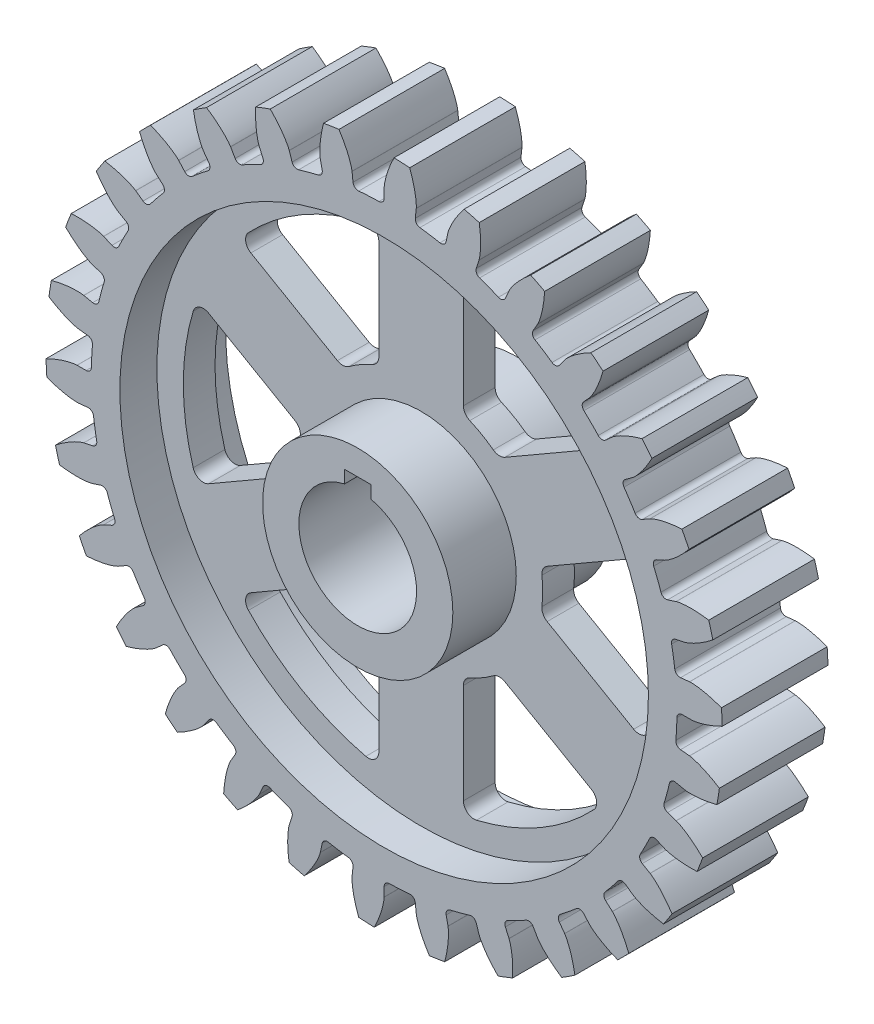
SolidWorks part; units mm, degrees
ref_plane "Front Plane" through (0, 0, 0) normal (0, 0, 1) x (1, 0, 0)
ref_plane "Top Plane" through (0, 0, 0) normal (0, 1, 0) x (1, 0, 0)
ref_plane "Right Plane" through (0, 0, 0) normal (1, 0, 0) x (0, 0, -1)
sketch "Sketch1" plane through (0, 0, 0) normal (1, 0, 0) x (0, 0, -1)
  line L0 (-19.05, 0) -> (19.05, 0)
  line L1 (19.05, 0) -> (19.05, 22.86)
  line L2 (19.05, 22.86) -> (3.81, 22.86)
  line L3 (3.81, 22.86) -> (3.81, 63.5)
  line L4 (3.81, 63.5) -> (12.7, 63.5)
  line L5 (12.7, 63.5) -> (12.7, 70.358)
  line L6 (12.7, 70.358) -> (-12.7, 70.358)
  line L7 (0, 55) -> (0, -55) construction
  line L8 (55, 0) -> (-55, 0) construction
  line L9 (0, 0) -> (0, 70.358) construction
  line L10 (-19.05, 0) -> (-19.05, 22.86)
  line L11 (-19.05, 22.86) -> (-3.81, 22.86)
  line L12 (-3.81, 22.86) -> (-3.81, 63.5)
  line L13 (-3.81, 63.5) -> (-12.7, 63.5)
  line L14 (-12.7, 63.5) -> (-12.7, 70.358)
  dimension "D1" = 3.81
  dimension "D2" = 63.5
  dimension "D3" = 70.358
  dimension "D4" = 12.7
ref_axis "Axis1" through (0, 0, 20.955) along (0, 0, -1)
revolve "Revolve1" add sketch "Sketch1" angle 360 about axis through (0, 0, 20.955) along (0, 0, -1)
sketch "Sketch2" plane through (0, 0, 0) normal (0, 0, 1) x (1, 0, 0)
  line L0 (73.787, 0) -> (70.358, 0)
  line L1 (0, 0) -> (94.0494, 4.9289) construction
  line L2 (73.3828, 7.7128) -> (69.9726, 7.3544)
  arc A0 (81.2453, 2.3735) -> (81.0484, 6.132) centre (0, 0) ccw
  circle A1 centre (0, 0) radius 70.358 construction
  arc A2 (70.358, 0) -> (69.9726, 7.3544) centre (0, 0) ccw
  spline S0 degree 4 poles (73.787, 0) (73.8416, 0.0012) (73.9944, 0.008) (74.2828, 0.0349) (74.7515, 0.0989) (75.345, 0.2096) (76.1065, 0.3861) (76.9949, 0.6365) (77.9608, 0.9559) (78.9981, 1.3503) (80.0202, 1.7854) (81.0261, 2.2568) (82.0158, 2.7611) (83.1972, 3.4098) (84.592, 4.2449) (86.1811, 5.2931) (87.9419, 6.5808) (89.6733, 7.9733) (91.3432, 9.4391) (92.7509, 10.7796) (93.9201, 11.967) (94.8691, 12.9798) (95.614, 13.8045) (96.5255, 14.8499) (97.4145, 15.9197) (98.1892, 16.8948) (98.8659, 17.7823) (99.359, 18.4422) (99.8613, 19.1329) (100.322, 19.7792) (100.825, 20.5115) (101.2452, 21.1308) (101.7679, 21.9265) (102.1191, 22.4721) (102.7345, 23.4529) (103.1421, 24.1299) (103.5488, 24.8103) (103.7468, 25.157) (103.8765, 25.3798) knots 0 0 0 0 0 0.005377 0.015084 0.028532 0.04661 0.064855 0.092111 0.119476 0.146842 0.174209 0.201575 0.228941 0.256307 0.307035 0.361767 0.4165 0.471232 0.525964 0.580697 0.608063 0.635429 0.662795 0.690161 0.744894 0.77226 0.785943 0.799626 0.826992 0.854358 0.868042 0.881725 0.909091 0.931818 0.954545 0.977273 1 1 1 1 1 construction
  spline S1 degree 4 poles (73.787, 0) (73.8416, 0.0012) (73.9944, 0.008) (74.2828, 0.0349) (74.7515, 0.0989) (75.345, 0.2096) (76.1065, 0.3861) (76.9949, 0.6365) (77.9608, 0.9559) (78.9981, 1.3503) (79.9496, 1.7554) (80.6354, 2.074) (81.0655, 2.2839) (81.2453, 2.3735) knots 0 0 0 0 0 0.005377 0.015084 0.028532 0.04661 0.064855 0.092111 0.119476 0.146842 0.174209 0.194009 0.194009 0.194009 0.194009 0.194009
  spline S2 degree 4 poles (73.3828, 7.7128) (73.4372, 7.7174) (73.5899, 7.7266) (73.8795, 7.7299) (74.3523, 7.7153) (74.9541, 7.6672) (75.7299, 7.5713) (76.6397, 7.4152) (77.6336, 7.1984) (78.7065, 6.9146) (79.6951, 6.6113) (80.4105, 6.366) (80.8602, 6.2022) (81.0484, 6.132) knots 0 0 0 0 0 0.005377 0.015084 0.028532 0.04661 0.064855 0.092111 0.119476 0.146842 0.174209 0.194009 0.194009 0.194009 0.194009 0.194009
extrude "Boss-Extrude1" add sketch "Sketch2" along normal up to surface and the other way up to surface contours S2 A0 S1 L0 A2 L2
fillet "Fillet5" radius 1.27 2 edges at (73.3828, 7.7128, 0) (69.9726, 7.3544, 0)
fillet "Fillet6" radius 1.27 2 edges at (73.787, 0, 0) (70.358, 0, 0)
pattern_circular "CirPattern2" count 30 over 360 about axis through (0, 0, 20.955) along (0, 0, -1) of "Boss-Extrude1", "Fillet5", "Fillet6"
sketch "Sketch3" plane through (0, 0, 0) normal (0, 0, 1) x (1, 0, 0)
  line L0 (0, 16.83) -> (3.175, 16.83)
  line L1 (0, -20.955) -> (0, 20.955) construction
  line L2 (0, 16.83) -> (-3.175, 16.83)
  line L3 (3.175, 16.83) -> (3.175, 13.782)
  line L4 (-3.175, 16.83) -> (-3.175, 13.782)
  arc A0 (-3.175, 13.782) -> (3.175, 13.782) centre (0, 0) ccw
extrude "Cut-Extrude2" cut sketch "Sketch3" against normal through all and the other way through all
sketch "Sketch4" plane through (0, 0, 0) normal (0, 0, 1) x (1, 0, 0)
  line L0 (10.16, 45.3436) -> (10.16, 32.6436)
  line L2 (0, -20.955) -> (0, 20.955) construction
  line L3 (0, 0) -> (93.946, 54.2398) construction
  line L4 (36.8269, 32.9938) -> (21.429, 24.1038)
  line L5 (10.16, 45.3436) -> (10.16, 56.2396)
  line L6 (10.16, 32.6436) -> (10.16, 27.3861)
  line L7 (21.429, 24.1038) -> (18.6371, 22.4919)
  line L8 (36.8269, 32.9938) -> (43.625, 36.9186)
  arc A0 (18.6371, 22.4919) -> (10.16, 27.3861) centre (0, 0) ccw
  arc A2 (43.625, 36.9186) -> (10.16, 56.2396) centre (0, 0) ccw
  dimension "D1" = 10.16
  dimension "D2" = 10.16
extrude "Cut-Extrude3" cut sketch "Sketch4" against normal through all and the other way through all
fillet "Fillet7" radius 2.54 1 edges at (10.16, 56.2396, 0)
fillet "Fillet8" radius 2.54 1 edges at (10.16, 27.3861, 0)
fillet "Fillet9" radius 2.54 1 edges at (18.6371, 22.4919, 0)
fillet "Fillet10" radius 2.54 1 edges at (43.625, 36.9186, 0)
pattern_circular "CirPattern3" count 6 over 360 about axis through (0, 0, 0) along (0, 0, 1) of "Cut-Extrude3", "Fillet8", "Fillet10", "Fillet9", "Fillet7"
